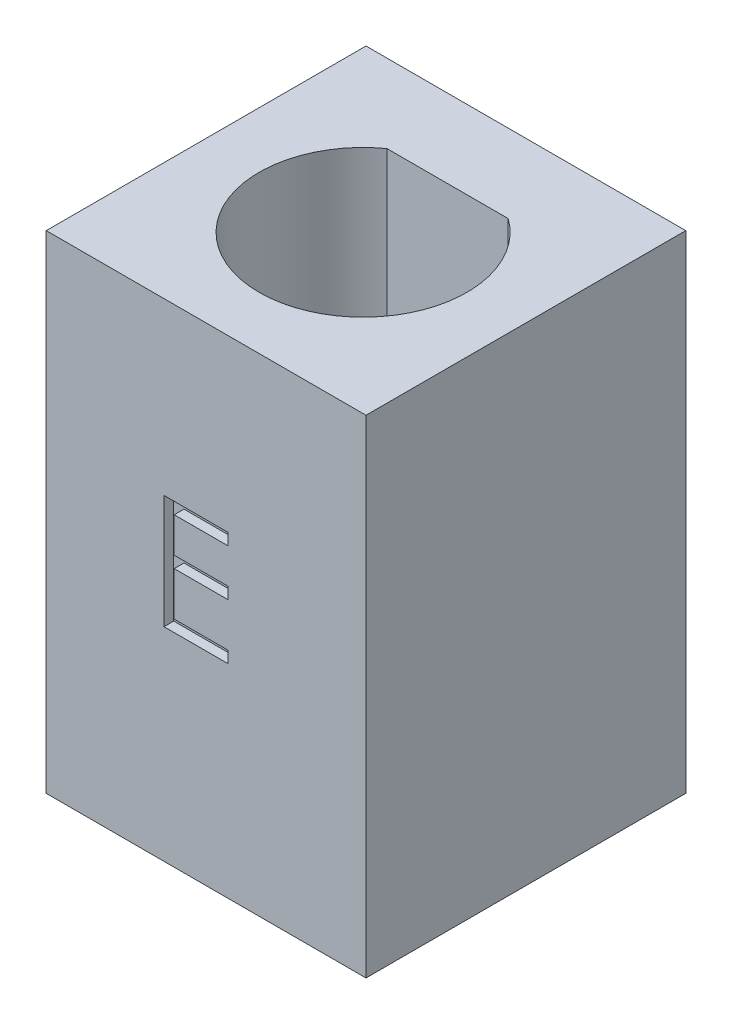
SolidWorks part; units mm, degrees
ref_plane "Front Plane" through (0, 0, 0) normal (0, 0, 1) x (1, 0, 0)
ref_plane "Top Plane" through (0, 0, 0) normal (0, 1, 0) x (1, 0, 0)
ref_plane "Right Plane" through (0, 0, 0) normal (1, 0, 0) x (0, 0, -1)
sketch "Sketch1" plane through (0, 0, 0) normal (0, 1, 0) x (1, 0, 0)
  line L0 (-1.8655, 2.5094) -> (1.8655, 2.5094)
  line L2 (-4.9207, 4.9207) -> (4.9207, 4.9207)
  line L3 (-4.9207, 4.9207) -> (-4.9207, -4.9207)
  line L4 (-4.9207, -4.9207) -> (4.9207, -4.9207)
  line L5 (4.9207, 4.9207) -> (4.9207, -4.9207)
  arc A1 (-1.8655, 2.5094) -> (1.8655, 2.5094) centre (0, -0.0906) ccw
  point P2 (0, 0)
  point P3 (0, 2.5094)
  dimension "D1" = 2.6
extrude "Boss-Extrude1" add sketch "Sketch1" along normal blind 15
sketch "Sketch2" plane through (0, 0, 4.9207) normal (0, 0, 1) x (1, 0, 0)
  text T0 "E"
extrude "Cut-Extrude1" cut sketch "Sketch2" against normal blind 0.3
